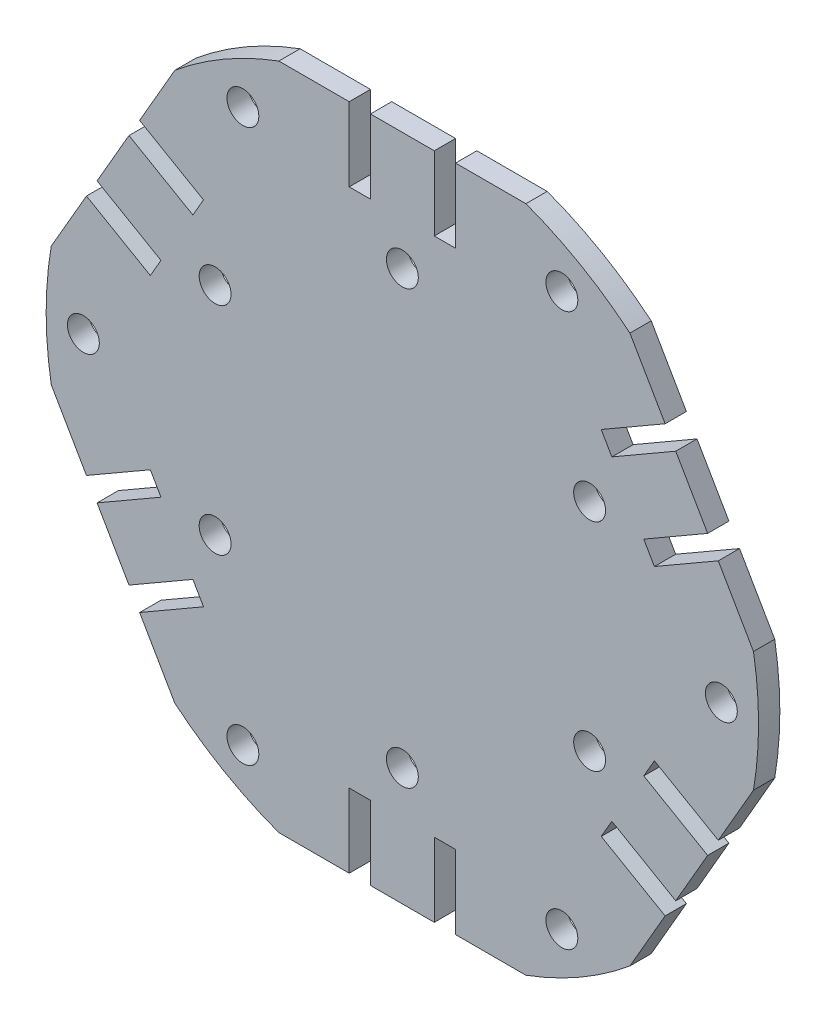
SolidWorks part; units mm, degrees
material "Acrylic (Medium-high impact)"
ref_plane "Front Plane" through (0, 0, 0) normal (0, 0, 1) x (1, 0, 0)
ref_plane "Top Plane" through (0, 0, 0) normal (0, 1, 0) x (1, 0, 0)
ref_plane "Right Plane" through (0, 0, 0) normal (1, 0, 0) x (0, 0, -1)
sketch "Model" plane through (0, 0, 0) normal (0, 0, 1) x (1, 0, 0)
  line L699 (-18.7014, -16.5708) -> (-19.7014, -14.8387)
  line L700 (-22.7014, -9.6426) -> (-23.7014, -7.9105)
  line L701 (-23.7014, -7.9105) -> (-29.7111, -11.3802)
  line L702 (-28.7111, -13.1122) -> (-22.7014, -9.6426)
  line L703 (-18.7014, -16.5708) -> (-24.7111, -20.0404)
  line L704 (-25.7111, -18.3084) -> (-19.7014, -14.8387)
  line L705 (-28.7111, -13.1122) -> (-25.7111, -18.3084)
  line L706 (-33.0204, -5.6482) -> (-29.7111, -11.3802)
  line L707 (-28.7111, -13.1122) -> (-25.7111, -18.3084)
  line L708 (-24.7111, -20.0404) -> (-21.4017, -25.7724)
  line L709 (-23.7014, 7.9105) -> (-22.7014, 9.6426)
  line L710 (-19.7014, 14.8387) -> (-18.7014, 16.5708)
  line L711 (-18.7014, 16.5708) -> (-24.7111, 20.0404)
  line L712 (-25.7111, 18.3084) -> (-19.7014, 14.8387)
  line L713 (-23.7014, 7.9105) -> (-29.7111, 11.3802)
  line L714 (-28.7111, 13.1122) -> (-22.7014, 9.6426)
  line L715 (-25.7111, 18.3084) -> (-28.7111, 13.1122)
  line L716 (-21.4017, 25.7724) -> (-24.7111, 20.0404)
  line L717 (-25.7111, 18.3084) -> (-28.7111, 13.1122)
  line L718 (-29.7111, 11.3802) -> (-33.0204, 5.6482)
  line L719 (5, -24.4813) -> (3, -24.4813)
  line L720 (-3, -24.4813) -> (-5, -24.4813)
  line L721 (-5, -24.4813) -> (-5, -31.4206)
  line L722 (-3, -31.4206) -> (-3, -24.4813)
  line L723 (5, -24.4813) -> (5, -31.4206)
  line L724 (3, -31.4206) -> (3, -24.4813)
  line L725 (-3, -31.4206) -> (3, -31.4206)
  line L726 (-11.6187, -31.4206) -> (-5, -31.4206)
  line L727 (-3, -31.4206) -> (3, -31.4206)
  line L728 (5, -31.4206) -> (11.6187, -31.4206)
  line L729 (23.7014, -7.9105) -> (22.7014, -9.6426)
  line L730 (19.7014, -14.8387) -> (18.7014, -16.5708)
  line L731 (18.7014, -16.5708) -> (24.7111, -20.0404)
  line L732 (25.7111, -18.3084) -> (19.7014, -14.8387)
  line L733 (23.7014, -7.9105) -> (29.7111, -11.3802)
  line L734 (28.7111, -13.1122) -> (22.7014, -9.6426)
  line L735 (25.7111, -18.3084) -> (28.7111, -13.1122)
  line L736 (21.4017, -25.7724) -> (24.7111, -20.0404)
  line L737 (25.7111, -18.3084) -> (28.7111, -13.1122)
  line L738 (29.7111, -11.3802) -> (33.0204, -5.6482)
  line L739 (-5, 24.4813) -> (-3, 24.4813)
  line L740 (3, 24.4813) -> (5, 24.4813)
  line L741 (5, 24.4813) -> (5, 31.4206)
  line L742 (3, 31.4206) -> (3, 24.4813)
  line L743 (-5, 24.4813) -> (-5, 31.4206)
  line L744 (-3, 31.4206) -> (-3, 24.4813)
  line L745 (3, 31.4206) -> (-3, 31.4206)
  line L746 (11.6187, 31.4206) -> (5, 31.4206)
  line L747 (3, 31.4206) -> (-3, 31.4206)
  line L748 (-5, 31.4206) -> (-11.6187, 31.4206)
  line L749 (23.7014, 7.9105) -> (22.7014, 9.6426)
  line L750 (19.7014, 14.8387) -> (18.7014, 16.5708)
  line L751 (18.7014, 16.5708) -> (24.7111, 20.0404)
  line L752 (25.7111, 18.3084) -> (19.7014, 14.8387)
  line L753 (23.7014, 7.9105) -> (29.7111, 11.3802)
  line L754 (28.7111, 13.1122) -> (22.7014, 9.6426)
  line L755 (25.7111, 18.3084) -> (28.7111, 13.1122)
  line L756 (21.4017, 25.7724) -> (24.7111, 20.0404)
  line L757 (25.7111, 18.3084) -> (28.7111, 13.1122)
  line L758 (29.7111, 11.3802) -> (33.0204, 5.6482)
  circle A324 centre (-17.6105, -10.1674) radius 1.5
  circle A325 centre (-17.6105, 10.1674) radius 1.5
  circle A326 centre (0, -20.3348) radius 1.5
  circle A327 centre (17.6105, -10.1674) radius 1.5
  circle A328 centre (0, 20.3348) radius 1.5
  arc A329 (33.0204, -5.6482) -> (33.0204, 5.6482) centre (0, 0) ccw
  arc A330 (21.4017, 25.7724) -> (11.6187, 31.4206) centre (0, 0) ccw
  arc A331 (-11.6187, 31.4206) -> (-21.4017, 25.7724) centre (0, 0) ccw
  arc A332 (-33.0204, 5.6482) -> (-33.0204, -5.6482) centre (0, 0) ccw
  arc A333 (-21.4017, -25.7724) -> (-11.6187, -31.4206) centre (0, 0) ccw
  arc A334 (11.6187, -31.4206) -> (21.4017, -25.7724) centre (0, 0) ccw
  circle A335 centre (-30, 0) radius 1.5
  circle A336 centre (-15, -25.9808) radius 1.5
  circle A337 centre (15, 25.9808) radius 1.5
  circle A338 centre (-15, 25.9808) radius 1.5
  circle A339 centre (15, -25.9808) radius 1.5
  circle A346 centre (30, 0) radius 1.5
  circle A349 centre (17.6105, 10.1674) radius 1.5
  dimension "D1" = 3
  dimension "D2" = 33.5
  dimension "D3" = 3
  dimension "D4" = 5
  dimension "D5" = 11.6187
  dimension "D6" = 15
  dimension "D7" = 17.6105
  dimension "D8" = 30
  dimension "D9" = 15
  dimension "D10" = 17.6105
  dimension "D11" = 18.7014
  dimension "D12" = 19.7014
  dimension "D13" = 30
  dimension "D14" = 10.1674
  dimension "D15" = 20.3348
  dimension "D16" = 25.9808
  dimension "D17" = 10.1674
  dimension "D18" = 20.3348
  dimension "D19" = 25.9808
extrude "Boss-Extrude1" add sketch "Model" along normal blind 2 contours L728 A334 L736 L731 L730 L732 L735 L734 L729 L733 L738 A329 L758 L753 L749 L754 L755 L752 L750 L751 L756 A330 L746 L741 L740 L742 L745 L744 L739 L743 L748 A331 L716 L711 L710 L712 L715 L714 L709 L713 L718 A332 L706 L701 L700 L702 L705 L704 L699 L703 L708
